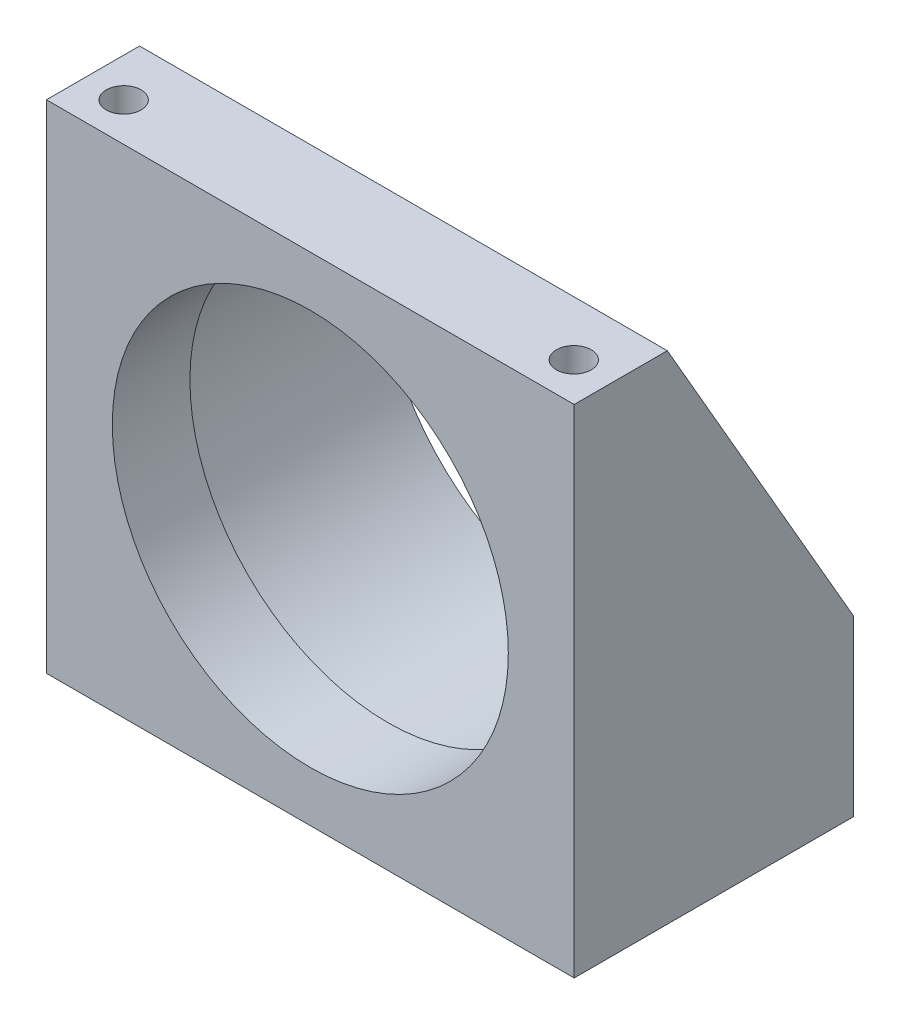
SolidWorks part; units mm, degrees
material "Alloy Steel"
ref_plane "Front Plane" through (0, 0, 0) normal (0, 0, 1) x (1, 0, 0)
ref_plane "Top Plane" through (0, 0, 0) normal (0, 1, 0) x (1, 0, 0)
ref_plane "Right Plane" through (0, 0, 0) normal (1, 0, 0) x (0, 0, -1)
sketch "Sketch1" plane through (0, 0, 0) normal (0, 0, 1) x (1, 0, 0)
  line L1 (-53.975, 101.6) -> (53.975, 101.6)
  line L2 (-53.975, 101.6) -> (-53.975, 0)
  line L3 (-53.975, 0) -> (53.975, 0)
  line L4 (53.975, 101.6) -> (53.975, 0)
  circle A0 centre (0, 50.8) radius 40.5003
  dimension "D4" = 81.0006
  dimension "D1" = 107.95
  dimension "D2" = 101.6
  dimension "D3" = 50.8
extrude "Extrude1" add sketch "Sketch1" against normal blind 57.15
sketch "Sketch2" plane through (53.975, 0, 0) normal (1, 0, 0) x (0, 0, -1)
  line L0 (19.05, 101.6) -> (57.15, 35.56)
  line L1 (0, 0) -> (0, 101.6) construction
  line L2 (57.15, 0) -> (0, 0) construction
  line L4 (0, 101.6) -> (0, 0)
  line L5 (0, 0) -> (57.15, 0)
  line L6 (57.15, 0) -> (57.15, 101.6)
  line L7 (57.15, 101.6) -> (0, 101.6)
  line L10 (57.15, 35.56) -> (57.15, 101.6)
  line L11 (57.15, 101.6) -> (19.05, 101.6)
  dimension "D2" = 19.05
  dimension "D3" = 35.56
  dimension "D1" = 0
extrude "Cut-Extrude1" cut sketch "Sketch2" against normal through all
sketch "Sketch3" plane through (0, 0, -57.15) normal (0, 0, -1) x (-1, 0, 0)
  circle A0 centre (0, 50.8) radius 42.926
  dimension "D1" = 85.852
extrude "Cut-Extrude2" cut sketch "Sketch3" against normal offset from surface (41.275 mm away) 15.875 up to face at (40.5003, 50.8, 0)
fillet "Fillet1" radius 1.524 1 edges at (42.926, 50.8, -15.875)
hole_wizard "Hole1" positions "Sketch5" profile "Sketch4" legacy end condition up to next
sketch "Sketch5" plane through (0, 101.6, 0) normal (0, 1, 0) x (-1, 0, 0)
  line L0 (-53.975, -19.05) -> (-53.975, 0) construction
  line L1 (-53.975, 0) -> (53.975, 0) construction
  point P0 (46.0502, -7.874)
  point P1 (-46.0248, -7.874)
  dimension "D1" = 7.9502
  dimension "D2" = 7.874
  dimension "D3" = 92.075
sketch "Sketch4" plane through (-46.0502, 101.6, -7.874) normal (1, 0, 0) x (0, 0, 1)
  line L0 (0, 0) -> (0, 101.6)
  line L1 (0, 101.6) -> (3.5687, 101.6)
  line L2 (3.5687, 101.6) -> (3.5687, 0)
  line L3 (3.5687, 0) -> (0, 0)
  line L4 (0, 110) -> (0, -10) construction
  dimension "Diameter" = 7.1374
  dimension "Depth" = 101.6
